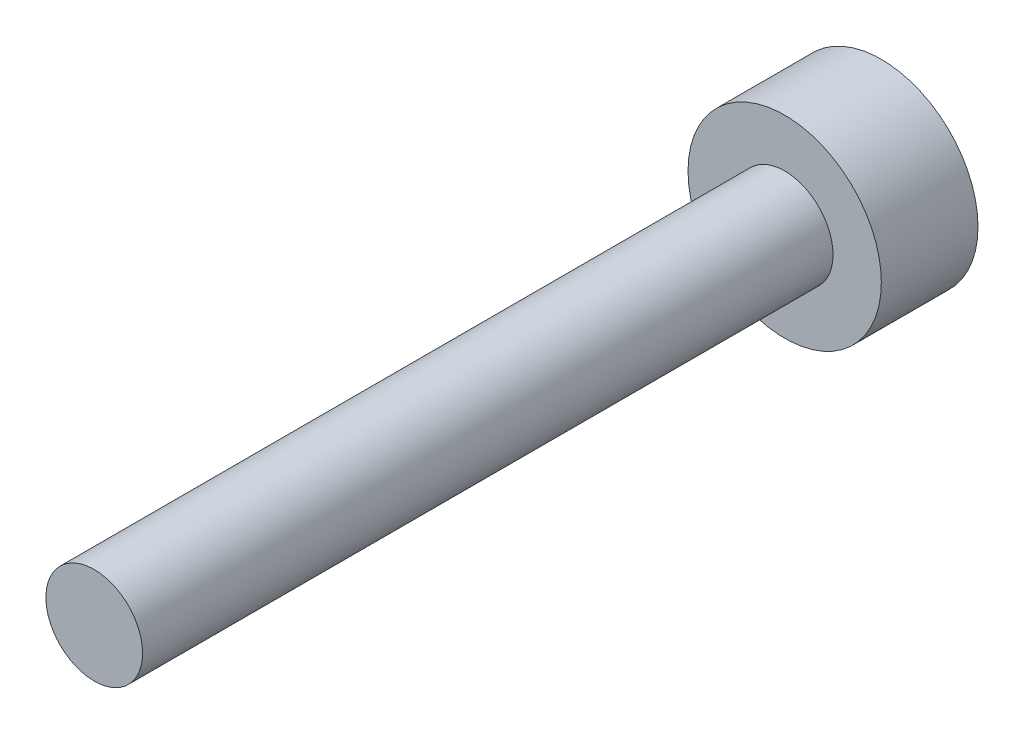
SolidWorks part; units mm, degrees
ref_plane "前视基准面" through (0, 0, 0) normal (0, 0, 1) x (1, 0, 0)
ref_plane "上视基准面" through (0, 0, 0) normal (0, 1, 0) x (1, 0, 0)
ref_plane "右视基准面" through (0, 0, 0) normal (1, 0, 0) x (0, 0, -1)
sketch "草图1" plane through (0, 0, 0) normal (0, 0, 1) x (1, 0, 0)
  circle A0 centre (0, 0) radius 1.4
extrude "凸台-拉伸1" add sketch "草图1" along normal blind 1.4
sketch "草图2" plane through (0, 0, 1.4) normal (0, 0, 1) x (1, 0, 0)
  circle A0 centre (0, 0) radius 0.7
extrude "凸台-拉伸2" add sketch "草图2" along normal blind 10
sketch "草图3" plane through (0, 0, 0) normal (0, 0, -1) x (-1, 0, 0)
  line L1 (0, 0.68) -> (-0.5889, 0.34)
  line L2 (-0.5889, 0.34) -> (-0.5889, -0.34)
  line L3 (-0.5889, -0.34) -> (0, -0.68)
  line L4 (0, -0.68) -> (0.5889, -0.34)
  line L5 (0.5889, -0.34) -> (0.5889, 0.34)
  line L6 (0.5889, 0.34) -> (0, 0.68)
  circle A1 centre (0, 0) radius 0.5889 construction
extrude "切除-拉伸1" cut sketch "草图3" against normal blind 1
